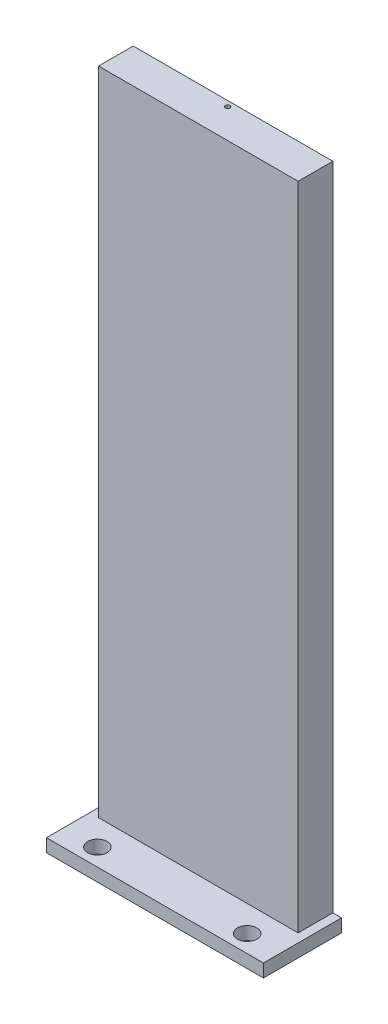
SolidWorks part; units mm, degrees
ref_plane "Front Plane" through (0, 0, 0) normal (0, 0, 1) x (1, 0, 0)
ref_plane "Top Plane" through (0, 0, 0) normal (0, 1, 0) x (1, 0, 0)
ref_plane "Right Plane" through (0, 0, 0) normal (1, 0, 0) x (0, 0, -1)
sketch "Sketch1" plane through (0, 0, 0) normal (0, 1, 0) x (1, 0, 0)
  line L1 (-7.2264, 4.3136) -> (42.7736, 4.3136)
  line L2 (-7.2264, 4.3136) -> (-7.2264, -3.6864)
  line L3 (-7.2264, -3.6864) -> (42.7736, -3.6864)
  line L4 (42.7736, 4.3136) -> (42.7736, -3.6864)
  dimension "D1" = 8
  dimension "D2" = 50
extrude "Boss-Extrude1" add sketch "Sketch1" along normal blind 3
hole_wizard "#8 Clearance Hole1" positions "3DSketch1" profile "Sketch2" hole size "#8" standard "ANSI Inch"
sketch3d "3DSketch1"
  line L0 (-7.2264, 3, -4.3136) -> (-7.2264, 3, 3.6864) construction
  line L1 (42.7736, 3, 3.6864) -> (42.7736, 3, -4.3136) construction
  line L2 (-7.2264, 3, 3.6864) -> (42.7736, 3, 3.6864) construction
  point P0 (0.5236, 3, -0.3136)
  point P2 (35.0236, 3, -0.3136)
  dimension "D1" = 7.75
  dimension "D2" = 7.75
  dimension "D3" = 4
  dimension "D4" = 4
  dimension "D7" = 34.5
sketch "Sketch2" plane through (0.5236, 3, -0.3136) normal (1, 0, 0) x (0, 0, 1)
  line L0 (0, 0) -> (0, 18.3507)
  line L1 (0, 18.3507) -> (2.2479, 17)
  line L2 (2.2479, 17) -> (2.2479, 0)
  line L5 (2.2479, 0) -> (0, 0)
  line L10 (0, 18.3507) -> (-2.2479, 17) construction
  line L11 (0, -6.35) -> (0, 107.95) construction
  dimension "Hole Dia." = 4.4958
  dimension "Hole Depth" = 17
  dimension "Drill Angle" = 118
sketch "Sketch3" plane through (0, 0, -4.3136) normal (0, 0, -1) x (-1, 0, 0)
  line L1 (7.2264, 0) -> (-42.7736, 0)
  line L2 (7.2264, 0) -> (7.2264, 3)
  line L3 (7.2264, 3) -> (-42.7736, 3)
  line L4 (-42.7736, 0) -> (-42.7736, 3)
extrude "Boss-Extrude2" add sketch "Sketch3" along normal blind 10
sketch "Sketch5" plane through (0, 3, 0) normal (0, 1, 0) x (1, 0, 0)
  line L0 (-7.2264, 14.3136) -> (42.7736, 14.3136) construction
  line L1 (-5.2264, 14.3136) -> (40.7736, 14.3136)
  line L2 (-5.2264, 14.3136) -> (-5.2264, 6.3136)
  line L3 (-5.2264, 6.3136) -> (40.7736, 6.3136)
  line L4 (40.7736, 14.3136) -> (40.7736, 6.3136)
  line L5 (-7.2264, 14.3136) -> (-7.2264, -3.6864) construction
  dimension "D1" = 8
  dimension "D2" = 2
  dimension "D3" = 2
extrude "Boss-Extrude3" add sketch "Sketch5" along normal blind 150
sketch "Sketch6" plane through (0, 153, 0) normal (0, 1, 0) x (1, 0, 0)
  line L0 (40.7736, 14.3136) -> (-5.2264, 14.3136) construction
  line L2 (-5.2264, 14.3136) -> (-5.2264, 6.3136) construction
  circle A0 centre (17.7736, 13.0636) radius 0.5207
  dimension "D1" = 1.25
  dimension "D2" = 23
extrude "Cut-Extrude1" cut sketch "Sketch6" against normal blind 30
